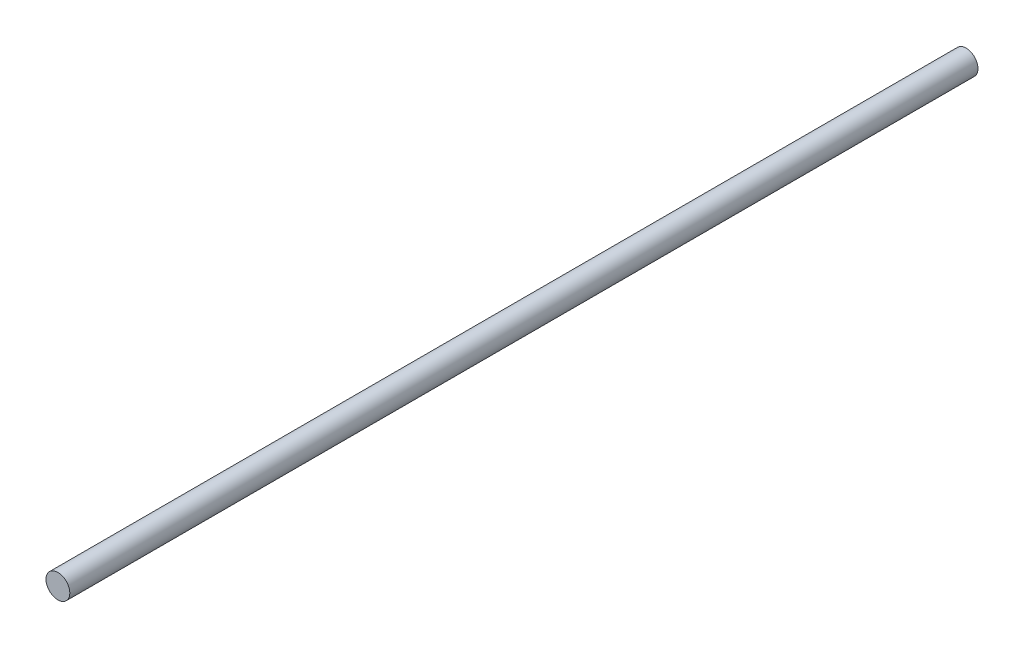
SolidWorks part; units mm, degrees
ref_plane "Front Plane" through (0, 0, 0) normal (0, 0, 1) x (1, 0, 0)
ref_plane "Top Plane" through (0, 0, 0) normal (0, 1, 0) x (1, 0, 0)
ref_plane "Right Plane" through (0, 0, 0) normal (1, 0, 0) x (0, 0, -1)
sketch "Esboço1" plane through (0, 0, 0) normal (0, 0, 1) x (1, 0, 0)
  circle A0 centre (-48.8753, 81.4072) radius 4
  dimension "D1" = 8
extrude "Ressalto-extrusão1" add sketch "Esboço1" along normal blind 305 contours A0
